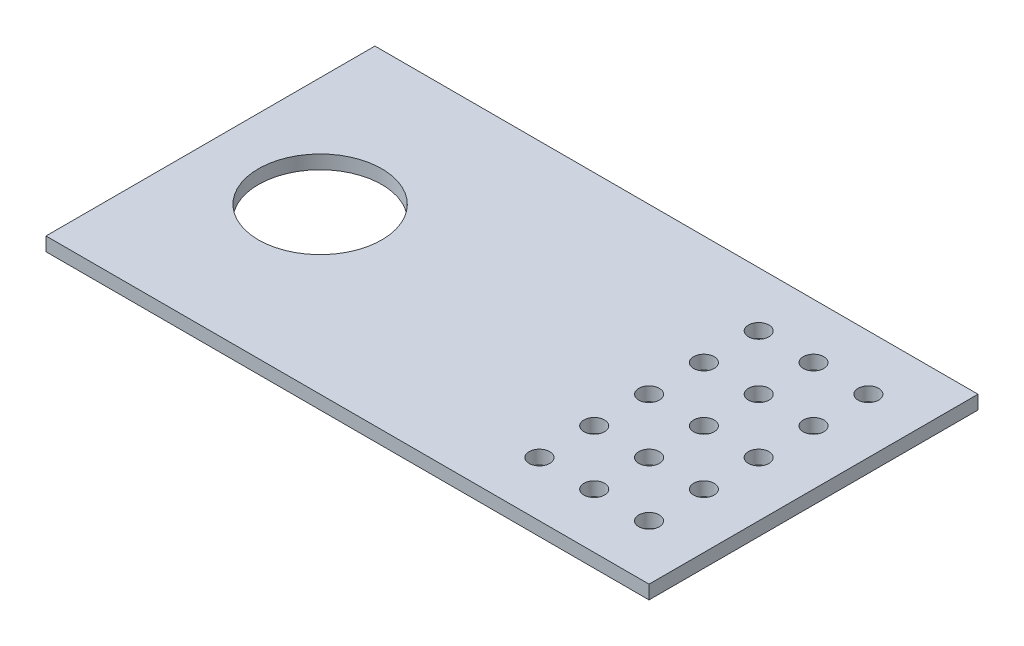
SolidWorks part; units mm, degrees
ref_plane "Front Plane" through (0, 0, 0) normal (0, 0, 1) x (1, 0, 0)
ref_plane "Top Plane" through (0, 0, 0) normal (0, 1, 0) x (1, 0, 0)
ref_plane "Right Plane" through (0, 0, 0) normal (1, 0, 0) x (0, 0, -1)
sketch "Sketch1" plane through (0, 0, 0) normal (0, 1, 0) x (1, 0, 0)
  line L1 (0, 0) -> (-139.7, 0)
  line L2 (0, 0) -> (0, 76.2)
  line L3 (0, 76.2) -> (-139.7, 76.2)
  line L4 (-139.7, 0) -> (-139.7, 76.2)
  circle A1 centre (-114.3, 38.1) radius 14.2875
  circle A2 centre (-38.1, 12.7) radius 2.3812
  circle A3 centre (-25.4, 12.7) radius 2.3812
  circle A4 centre (-12.7, 12.7) radius 2.3812
  circle A5 centre (-25.4, 25.4) radius 2.3812
  circle A6 centre (-12.7, 25.4) radius 2.3813
  circle A7 centre (-25.4, 38.1) radius 2.3812
  circle A8 centre (-12.7, 38.1) radius 2.3812
  circle A9 centre (-25.4, 50.8) radius 2.3812
  circle A10 centre (-12.7, 50.8) radius 2.3812
  circle A11 centre (-25.4, 63.5) radius 2.3813
  circle A12 centre (-12.7, 63.5) radius 2.3813
  circle A13 centre (-38.1, 25.4) radius 2.3812
  circle A14 centre (-38.1, 38.1) radius 2.3812
  circle A15 centre (-38.1, 50.8) radius 2.3812
  circle A16 centre (-38.1, 63.5) radius 2.3812
  point P9 (-24.5926, 25.3936)
  point P11 (-139.7, 38.1)
  dimension "D1" = 28.575
  dimension "D5" = 4.7625
  dimension "D2" = 114.3
  dimension "D3" = 139.7
  dimension "D4" = 12.7
  dimension "D6" = 76.2
  dimension "D7" = 76.2
  dimension "D10" = 12.7
  dimension "D11" = 12.7
  dimension "D8" = 3
  dimension "D9" = 5
extrude "Boss-Extrude1" add sketch "Sketch1" along normal blind 3.175
